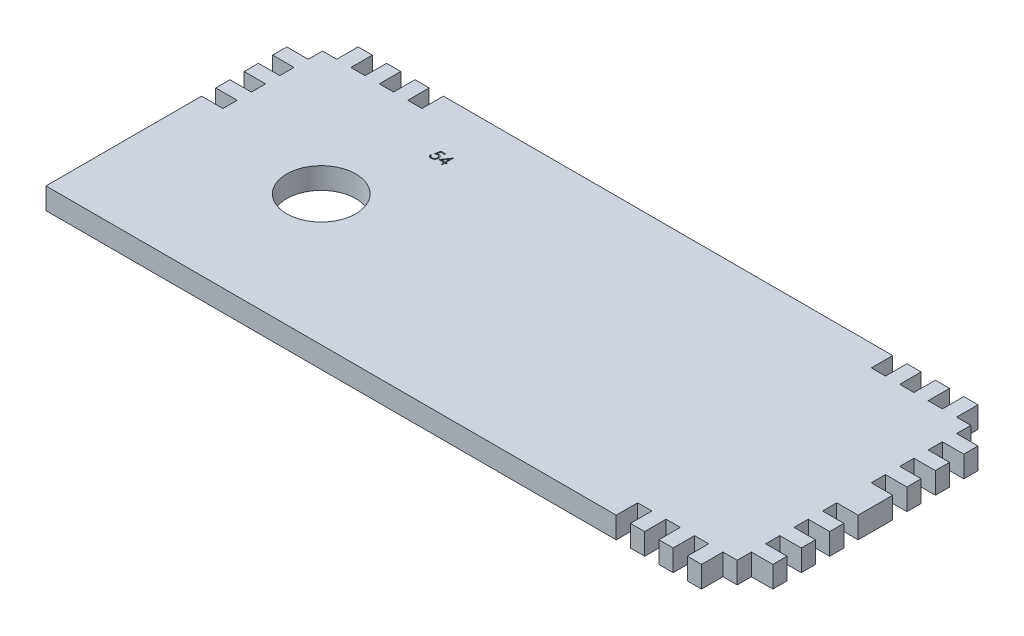
SolidWorks part; units mm, degrees
material "Acrylic (Medium-high impact)"
ref_plane "Front Plane" through (0, 0, 0) normal (0, 0, 1) x (1, 0, 0)
ref_plane "Top Plane" through (0, 0, 0) normal (0, 1, 0) x (1, 0, 0)
ref_plane "Right Plane" through (0, 0, 0) normal (1, 0, 0) x (0, 0, -1)
sketch "Sketch1" plane through (0, 0, 0) normal (0, 1, 0) x (1, 0, 0)
  line L1 (0, 0) -> (200, 0)
  line L2 (0, 0) -> (0, 80)
  line L3 (0, 80) -> (200, 80)
  line L4 (200, 0) -> (200, 80)
  line L9 (181.458, 6.2) -> (185.572, 6.2)
  line L10 (181.458, 6.2) -> (181.458, 0)
  line L11 (181.458, 0) -> (185.572, 0)
  line L12 (185.572, 6.2) -> (185.572, 0)
  line L13 (173.23, 6.2) -> (177.344, 6.2)
  line L14 (173.23, 6.2) -> (173.23, 0)
  line L15 (173.23, 0) -> (177.344, 0)
  line L16 (177.344, 6.2) -> (177.344, 0)
  line L21 (165.002, 0) -> (169.116, 0)
  line L22 (165.002, 0) -> (165.002, 6.2)
  line L23 (165.002, 6.2) -> (169.116, 6.2)
  line L24 (169.116, 0) -> (169.116, 6.2)
  line L29 (200, 14.428) -> (193.8, 14.428)
  line L30 (200, 14.428) -> (200, 18.542)
  line L31 (200, 18.542) -> (193.8, 18.542)
  line L32 (193.8, 14.428) -> (193.8, 18.542)
  line L41 (200, 22.656) -> (193.8, 22.656)
  line L42 (200, 22.656) -> (200, 26.77)
  line L43 (200, 26.77) -> (193.8, 26.77)
  line L44 (193.8, 22.656) -> (193.8, 26.77)
  line L45 (200, 30.884) -> (193.8, 30.884)
  line L46 (200, 30.884) -> (200, 34.998)
  line L47 (200, 34.998) -> (193.8, 34.998)
  line L48 (193.8, 30.884) -> (193.8, 34.998)
  line L53 (0, 69.686) -> (6.2, 69.686)
  line L54 (0, 69.686) -> (0, 80)
  line L55 (0, 80) -> (6.2, 80)
  line L56 (6.2, 69.686) -> (6.2, 80)
  line L57 (14.428, 80) -> (18.542, 80)
  line L58 (14.428, 80) -> (14.428, 73.8)
  line L59 (14.428, 73.8) -> (18.542, 73.8)
  line L60 (18.542, 80) -> (18.542, 73.8)
  line L61 (22.656, 80) -> (26.77, 80)
  line L62 (22.656, 80) -> (22.656, 73.8)
  line L63 (22.656, 73.8) -> (26.77, 73.8)
  line L64 (26.77, 80) -> (26.77, 73.8)
  line L65 (0, 65.572) -> (6.2, 65.572)
  line L66 (0, 65.572) -> (0, 61.458)
  line L67 (0, 61.458) -> (6.2, 61.458)
  line L68 (6.2, 65.572) -> (6.2, 61.458)
  line L69 (30.884, 80) -> (34.998, 80)
  line L70 (30.884, 80) -> (30.884, 73.8)
  line L71 (30.884, 73.8) -> (34.998, 73.8)
  line L72 (34.998, 80) -> (34.998, 73.8)
  line L73 (0, 57.344) -> (6.2, 57.344)
  line L74 (0, 57.344) -> (0, 53.23)
  line L75 (0, 53.23) -> (6.2, 53.23)
  line L76 (6.2, 57.344) -> (6.2, 53.23)
  line L77 (0, 49.116) -> (6.2, 49.116)
  line L78 (0, 49.116) -> (0, 45.002)
  line L79 (0, 45.002) -> (6.2, 45.002)
  line L80 (6.2, 49.116) -> (6.2, 45.002)
  line L85 (193.8, 10.314) -> (200, 10.314)
  line L86 (193.8, 10.314) -> (193.8, 0)
  line L87 (193.8, 0) -> (200, 0)
  line L88 (200, 10.314) -> (200, 0)
  line L89 (189.686, 6.2) -> (200, 6.2)
  line L90 (189.686, 6.2) -> (189.686, 0)
  line L91 (189.686, 0) -> (200, 0)
  line L92 (200, 6.2) -> (200, 0)
  line L93 (0, 80) -> (10.314, 80)
  line L94 (0, 80) -> (0, 73.8)
  line L95 (0, 73.8) -> (10.314, 73.8)
  line L96 (10.314, 80) -> (10.314, 73.8)
  line L101 (189.686, 80) -> (200, 80)
  line L102 (189.686, 80) -> (189.686, 73.8)
  line L103 (189.686, 73.8) -> (200, 73.8)
  line L104 (200, 80) -> (200, 73.8)
  line L105 (200, 80) -> (193.8, 80)
  line L106 (200, 80) -> (200, 69.686)
  line L107 (200, 69.686) -> (193.8, 69.686)
  line L108 (193.8, 80) -> (193.8, 69.686)
  line L109 (185.576, 80) -> (181.462, 80)
  line L110 (185.576, 80) -> (185.576, 73.8)
  line L111 (185.576, 73.8) -> (181.462, 73.8)
  line L112 (181.462, 80) -> (181.462, 73.8)
  line L113 (177.348, 80) -> (173.234, 80)
  line L114 (177.348, 80) -> (177.348, 73.8)
  line L115 (177.348, 73.8) -> (173.234, 73.8)
  line L116 (173.234, 80) -> (173.234, 73.8)
  line L117 (169.12, 80) -> (165.006, 80)
  line L118 (169.12, 80) -> (169.12, 73.8)
  line L119 (169.12, 73.8) -> (165.006, 73.8)
  line L120 (165.006, 80) -> (165.006, 73.8)
  line L121 (200, 65.572) -> (193.8, 65.572)
  line L122 (200, 65.572) -> (200, 61.458)
  line L123 (200, 61.458) -> (193.8, 61.458)
  line L124 (193.8, 65.572) -> (193.8, 61.458)
  line L125 (200, 57.344) -> (193.8, 57.344)
  line L126 (200, 57.344) -> (200, 53.23)
  line L127 (200, 53.23) -> (193.8, 53.23)
  line L128 (193.8, 57.344) -> (193.8, 53.23)
  line L129 (200, 49.116) -> (193.8, 49.116)
  line L130 (200, 49.116) -> (200, 45.002)
  line L131 (200, 45.002) -> (193.8, 45.002)
  line L132 (193.8, 49.116) -> (193.8, 45.002)
  circle A0 centre (41.8112, 37.8364) radius 10
  point P5 (41.8112, 37.8364)
  dimension "D49" = 6.2
  dimension "D1" = 200
  dimension "D2" = 80
  dimension "D5" = 6.2
  dimension "D6" = 4.114
  dimension "D7" = 6.2
  dimension "D8" = 4.114
  dimension "D9" = 4.114
  dimension "D10" = 6.2
  dimension "D11" = 4.114
  dimension "D12" = 4.114
  dimension "D13" = 6.2
  dimension "D14" = 10.314
  dimension "D15" = 4.114
  dimension "D16" = 4.114
  dimension "D17" = 4.114
  dimension "D18" = 6.2
  dimension "D19" = 4.114
  dimension "D20" = 6.2
  dimension "D21" = 4.114
  dimension "D22" = 4.114
  dimension "D23" = 6.2
  dimension "D24" = 4.114
  dimension "D25" = 4.114
  dimension "D26" = 6.2
  dimension "D27" = 10.314
  dimension "D28" = 6.2
  dimension "D29" = 4.114
  dimension "D30" = 4.114
  dimension "D31" = 6.2
  dimension "D32" = 4.114
  dimension "D33" = 6.2
  dimension "D34" = 4.114
  dimension "D35" = 4.114
  dimension "D36" = 4.114
  dimension "D37" = 6.2
  dimension "D38" = 10.314
  dimension "D39" = 4.114
  dimension "D40" = 6.2
  dimension "D41" = 6.2
  dimension "D42" = 4.114
  dimension "D43" = 4.114
  dimension "D44" = 4.114
  dimension "D45" = 4.114
  dimension "D46" = 6.2
  dimension "D47" = 6.2
  dimension "D48" = 10.314
  dimension "D50" = 10.314
  dimension "D51" = 10.314
  dimension "D52" = 6.2
  dimension "D53" = 4.11
  dimension "D54" = 4.114
  dimension "D55" = 4.114
  dimension "D56" = 6.2
  dimension "D57" = 6.2
  dimension "D58" = 6.2
  dimension "D59" = 6.2
  dimension "D60" = 4.114
  dimension "D61" = 4.114
  dimension "D62" = 4.114
  dimension "D63" = 4.114
  dimension "D64" = 4.114
  dimension "D65" = 4.114
  dimension "D66" = 6.2
  dimension "D67" = 4.114
  dimension "D68" = 4.114
  dimension "D69" = 4.114
  dimension "D70" = 6.2
extrude "Boss-Extrude1" add sketch "Sketch1" along normal blind 6.2
sketch "Sketch2" plane through (0, 6.2, 0) normal (0, 1, 0) x (1, 0, 0)
  text T0 "54"
extrude "Cut-Extrude1" cut sketch "Sketch2" against normal blind 1
